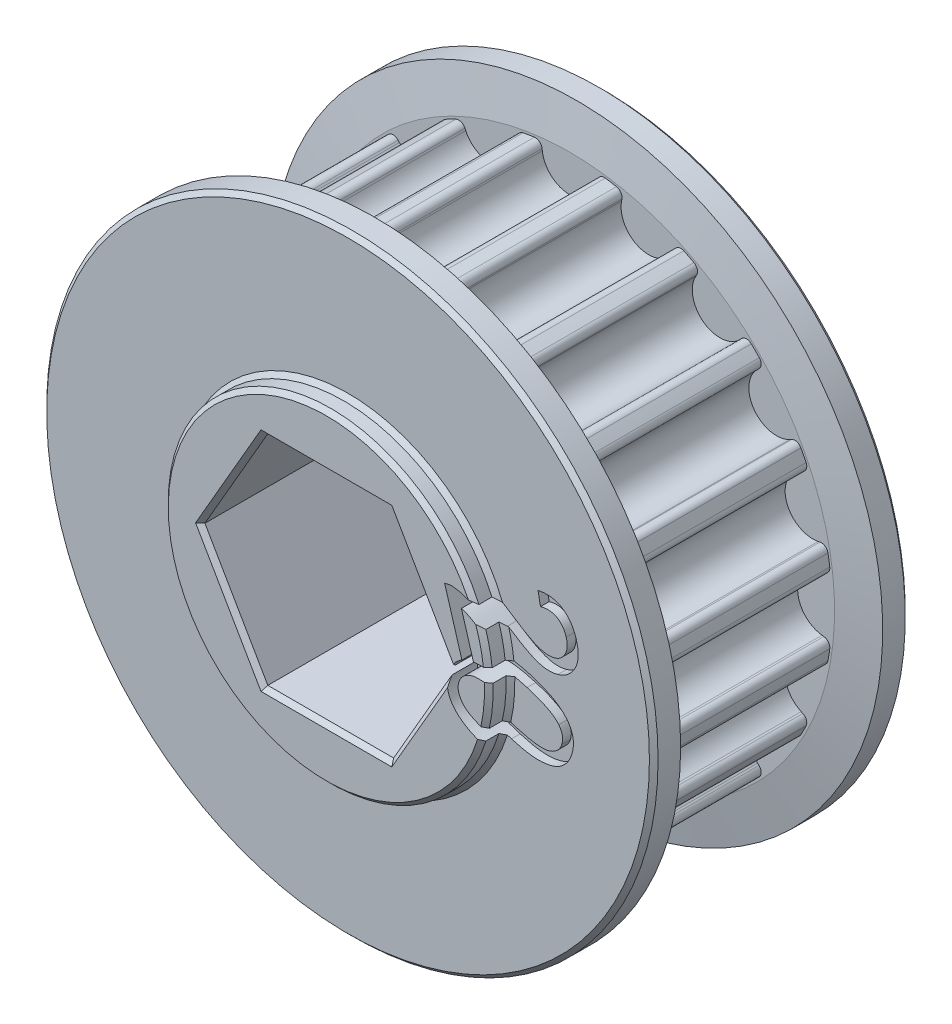
SolidWorks part; units mm, degrees
material "ABS"
ref_plane "Front Plane" through (0, 0, 0) normal (0, 0, 1) x (1, 0, 0)
ref_plane "Top Plane" through (0, 0, 0) normal (0, 1, 0) x (1, 0, 0)
ref_plane "Right Plane" through (0, 0, 0) normal (1, 0, 0) x (0, 0, -1)
sketch "Sketch2" plane through (0, 0, 0) normal (0, 0, 1) x (1, 0, 0)
  circle A0 centre (0, 0) radius 15.3811
extrude "pulley" add sketch "Sketch2" along normal mid plane 11
sketch "tooth" plane through (0, 0, 0) normal (0, 0, 1) x (1, 0, 0)
  line L0 (0, 0) -> (0, 14.9811) construction
  line L1 (4.9299, 14.1467) -> (0, 14.9811) construction
  line L2 (4.9299, 14.1467) -> (0, 0) construction
  line L3 (-2.1327, 19.0167) -> (-1.6129, 14.7831)
  line L6 (2.1327, 19.0167) -> (1.6129, 14.7831)
  line L7 (-2.1327, 19.0167) -> (2.1327, 19.0167)
  arc A1 (-1.6129, 14.7831) -> (1.6129, 14.7831) centre (0, 14.9811) ccw
  arc A2 (0, 14.9811) -> (4.9299, 14.1467) centre (0, 0) cw construction
  circle A3 centre (4.9299, 14.1467) radius 1.625 construction
extrude "cut tooth" cut sketch "tooth" against normal mid plane 11
fillet "blend tooth" radius 0.4 2 edges at (1.6751, 15.2896, 0) (-1.6751, 15.2896, 0)
pattern_circular "tooth pattern" count 20 over 360 about axis through (0, 0, 0) along (0, 0, 1) of "cut tooth", "blend tooth"
sketch "Sketch3" plane through (0, 0, 0) normal (0, 0, 1) x (1, 0, 0)
  circle A0 centre (0, 0) radius 17.9211
  circle A1 centre (0, 0) radius 15.3811 construction
  dimension "D1" = 2.54
extrude "sidewall" add sketch "Sketch3" along normal blind 2 from offset 5.5
mirror "mirror sidewall" about plane through (0, 0, 0) normal (0, 0, 1) of "sidewall"
chamfer "sidewall chamfer" distance 2.4 angle 10 2 edges at (17.9211, 0, 5.5) (17.9211, 0, -5.5)
sketch "Sketch5" plane through (0, 0, 0) normal (0, 0, 1) x (1, 0, 0)
  circle A0 centre (0, 0) radius 9.525
  dimension "D1" = 19.05
extrude "bearing spacer (Manual Suppress)" add sketch "Sketch5" along normal blind 8.77 and the other way blind 8.77
sketch "Sketch4" plane through (0, 0, 0) normal (0, 0, 1) x (1, 0, 0)
  line L1 (3.6882, 6.3881) -> (-3.6882, 6.3881)
  line L2 (-3.6882, 6.3881) -> (-7.3763, 0)
  line L3 (-7.3763, 0) -> (-3.6882, -6.3881)
  line L4 (-3.6882, -6.3881) -> (3.6882, -6.3881)
  line L5 (3.6882, -6.3881) -> (7.3763, 0)
  line L6 (7.3763, 0) -> (3.6882, 6.3881)
  circle A0 centre (0, 0) radius 6.3881 construction
  dimension "D1" = 12.7762
extrude "hex shaft" cut sketch "Sketch4" against normal mid plane 127
chamfer "chamfers" distance 0.254 angle 45 18 edges at (17.9211, 0, -7.5) (17.9211, 0, 7.5) (-9.525, 0, -7.5) (9.525, 0, 7.5) (9.525, 0, 8.77) (0, 6.3881, 8.77) (-5.5323, 3.194, 8.77) (-5.5323, -3.194, 8.77) (0, -6.3881, 8.77) (5.5323, -3.194, 8.77) (5.5323, 3.1941, 8.77) (9.525, 0, -8.77) (0, -6.3881, -8.77) (-5.5323, -3.194, -8.77) (-5.5323, 3.194, -8.77) (0, 6.3881, -8.77) (5.5323, 3.1941, -8.77) (5.5323, -3.194, -8.77)
sketch "SK-VersaCut" plane through (0, 0, 0) normal (0, 0, 1) x (1, 0, 0)
  line B0 (6.3387, 23.6565) -> (5.299, 19.7762)
  line B1 (14.4772, 14.4772) -> (17.3177, 17.3177)
  line B2 (23.6565, 6.3387) -> (19.7762, 5.299)
  line B3 (19.7762, -5.299) -> (23.6565, -6.3387)
  line B4 (17.3177, -17.3177) -> (14.4772, -14.4772)
  line B5 (5.299, -19.7762) -> (6.3387, -23.6565)
  line B6 (-6.3387, -23.6565) -> (-5.299, -19.7762)
  line B7 (-14.4772, -14.4772) -> (-17.3177, -17.3177)
  line B8 (-23.6565, -6.3387) -> (-19.7762, -5.299)
  line B9 (-19.7762, 5.299) -> (-23.6565, 6.3387)
  line B10 (-17.3177, 17.3177) -> (-14.4772, 14.4772)
  line B11 (-5.299, 19.7762) -> (-6.3387, 23.6565)
  circle B12 centre (0, 23.8125) radius 2.2479
  arc B13 (5.9535, 18.5765) -> (13.1109, 14.4442) centre (0, 0) cw
  arc B14 (7.5904, 24.3458) -> (17.2889, 18.7464) centre (0, 0) cw
  arc B15 (5.9535, 18.5765) -> (5.299, 19.7762) centre (6.2559, 19.5198) cw
  arc B16 (13.1109, 14.4442) -> (14.4772, 14.4772) centre (13.7767, 15.1777) ccw
  arc B17 (17.2889, 18.7464) -> (17.3177, 17.3177) centre (16.6173, 18.0182) cw
  arc B18 (7.5904, 24.3458) -> (6.3387, 23.6565) centre (7.2956, 23.4001) ccw
  circle B19 centre (20.6222, 11.9062) radius 2.2479
  arc B20 (19.0645, 4.1323) -> (19.0645, -4.1323) centre (0, 0) cw
  arc B21 (24.8793, 5.5994) -> (24.8793, -5.5994) centre (0, 0) cw
  arc B22 (19.0645, 4.1323) -> (19.7762, 5.299) centre (20.0326, 4.3422) cw
  arc B23 (19.0645, -4.1323) -> (19.7762, -5.299) centre (20.0326, -4.3422) ccw
  arc B24 (24.8793, -5.5994) -> (23.6565, -6.3387) centre (23.9129, -5.3819) cw
  arc B25 (24.8793, 5.5994) -> (23.6565, 6.3387) centre (23.9129, 5.3819) ccw
  circle B26 centre (20.6222, -11.9063) radius 2.2479
  arc B27 (13.1109, -14.4442) -> (5.9535, -18.5765) centre (0, 0) cw
  arc B28 (17.2889, -18.7464) -> (7.5904, -24.3458) centre (0, 0) cw
  arc B29 (13.1109, -14.4442) -> (14.4772, -14.4772) centre (13.7767, -15.1777) cw
  arc B30 (5.9535, -18.5765) -> (5.299, -19.7762) centre (6.2559, -19.5198) ccw
  arc B31 (7.5904, -24.3458) -> (6.3387, -23.6565) centre (7.2956, -23.4001) cw
  arc B32 (17.2889, -18.7464) -> (17.3177, -17.3177) centre (16.6173, -18.0182) ccw
  circle B33 centre (0, -23.8125) radius 2.2479
  arc B34 (-5.9535, -18.5765) -> (-13.1109, -14.4442) centre (0, 0) cw
  arc B35 (-7.5904, -24.3458) -> (-17.2889, -18.7464) centre (0, 0) cw
  arc B36 (-5.9535, -18.5765) -> (-5.299, -19.7762) centre (-6.2559, -19.5198) cw
  arc B37 (-13.1109, -14.4442) -> (-14.4772, -14.4772) centre (-13.7767, -15.1777) ccw
  arc B38 (-17.2889, -18.7464) -> (-17.3177, -17.3177) centre (-16.6173, -18.0182) cw
  arc B39 (-7.5904, -24.3458) -> (-6.3387, -23.6565) centre (-7.2956, -23.4001) ccw
  circle B40 centre (-20.6222, -11.9063) radius 2.2479
  arc B41 (-19.0645, -4.1323) -> (-19.0645, 4.1323) centre (0, 0) cw
  arc B42 (-24.8793, -5.5994) -> (-24.8793, 5.5994) centre (0, 0) cw
  arc B43 (-19.0645, -4.1323) -> (-19.7762, -5.299) centre (-20.0326, -4.3422) cw
  arc B44 (-19.0645, 4.1323) -> (-19.7762, 5.299) centre (-20.0326, 4.3422) ccw
  arc B45 (-24.8793, 5.5994) -> (-23.6565, 6.3387) centre (-23.9129, 5.3819) cw
  arc B46 (-24.8793, -5.5994) -> (-23.6565, -6.3387) centre (-23.9129, -5.3819) ccw
  circle B47 centre (-20.6222, 11.9063) radius 2.2479
  arc B48 (-13.1109, 14.4442) -> (-5.9535, 18.5765) centre (0, 0) cw
  arc B49 (-17.2889, 18.7464) -> (-7.5904, 24.3458) centre (0, 0) cw
  arc B50 (-13.1109, 14.4442) -> (-14.4772, 14.4772) centre (-13.7767, 15.1777) cw
  arc B51 (-5.9535, 18.5765) -> (-5.299, 19.7762) centre (-6.2559, 19.5198) ccw
  arc B52 (-7.5904, 24.3458) -> (-6.3387, 23.6565) centre (-7.2956, 23.4001) cw
  arc B53 (-17.2889, 18.7464) -> (-17.3177, 17.3177) centre (-16.6173, 18.0182) ccw
sketch_block_instance "VersaKey-1"
sketch_block "Block1" parameters "D1"=47.625, "D2"=4.4958, "D3"=19.5072, "D4"=25.5016, "D6"=0.9906, "D5"=30
extrude "VersaKey (Manual Suppress)" [suppressed] cut sketch "SK-VersaCut" against normal through all both and the other way through all
sketch "Lightening Holes" plane through (0, 0, 0) normal (0, 0, 1) x (1, 0, 0)
  line L0 (-2.1942, 8.8805) -> (-3.9521, 11.9253)
  line L1 (3.9521, 11.9253) -> (2.1942, 8.8805)
  line L14 (0, 0) -> (-3.6662, 6.35) construction
  line L15 (0, 0) -> (0, 6.35) construction
  line L24 (0, 0) -> (3.6662, 6.35) construction
  line L25 (0, 6.35) -> (-3.6662, 6.35) construction
  line L26 (0, 6.35) -> (3.6662, 6.35) construction
  line L27 (-3.0943, 11.43) -> (3.0943, 11.43)
  line L28 (0, 6.35) -> (0, 11.43) construction
  line L29 (6.5936, 6.3405) -> (8.3515, 9.3853)
  line L30 (8.3515, 8.3947) -> (11.4458, 3.0353)
  line L31 (12.3037, 2.54) -> (8.7878, 2.54)
  line L32 (8.7878, -2.54) -> (12.3037, -2.54)
  line L33 (11.4458, -3.0353) -> (8.3515, -8.3947)
  line L34 (8.3515, -9.3853) -> (6.5936, -6.3405)
  line L35 (2.1942, -8.8805) -> (3.9521, -11.9253)
  line L36 (3.0943, -11.43) -> (-3.0943, -11.43)
  line L37 (-3.9521, -11.9253) -> (-2.1942, -8.8805)
  line L38 (-6.5936, -6.3405) -> (-8.3515, -9.3853)
  line L39 (-8.3515, -8.3947) -> (-11.4458, -3.0353)
  line L40 (-12.3037, -2.54) -> (-8.7878, -2.54)
  line L41 (-8.7878, 2.54) -> (-12.3037, 2.54)
  line L42 (-11.4458, 3.0353) -> (-8.3515, 8.3947)
  line L43 (-8.3515, 9.3853) -> (-6.5936, 6.3405)
  arc A3 (-1.4761, 10.3565) -> (1.4761, 10.3565) centre (0, 0) cw
  arc A4 (-3.0943, 11.43) -> (-3.9521, 11.9253) centre (-3.0943, 12.4206) cw
  arc A5 (3.0943, 11.43) -> (3.9521, 11.9253) centre (3.0943, 12.4206) ccw
  arc A6 (1.4761, 10.3565) -> (2.1942, 8.8805) centre (1.3363, 9.3758) cw
  arc A7 (-1.4761, 10.3565) -> (-2.1942, 8.8805) centre (-1.3363, 9.3758) ccw
  arc A72 (8.2309, 6.4566) -> (9.707, 3.8999) centre (0, 0) cw
  arc A73 (8.2309, 6.4566) -> (6.5936, 6.3405) centre (7.4515, 5.8452) ccw
  arc A74 (8.3515, 8.3947) -> (8.3515, 9.3853) centre (9.2094, 8.89) cw
  arc A75 (9.707, 3.8999) -> (8.7878, 2.54) centre (8.7878, 3.5306) cw
  arc A76 (9.707, -3.8999) -> (8.2309, -6.4566) centre (0, 0) cw
  arc A77 (9.707, -3.8999) -> (8.7878, -2.54) centre (8.7878, -3.5306) ccw
  arc A78 (11.4458, -3.0353) -> (12.3037, -2.54) centre (12.3037, -3.5306) cw
  arc A79 (8.2309, -6.4566) -> (6.5936, -6.3405) centre (7.4515, -5.8452) cw
  arc A80 (1.4761, -10.3565) -> (-1.4761, -10.3565) centre (0, 0) cw
  arc A81 (1.4761, -10.3565) -> (2.1942, -8.8805) centre (1.3363, -9.3758) ccw
  arc A82 (3.0943, -11.43) -> (3.9521, -11.9253) centre (3.0943, -12.4206) cw
  arc A83 (-1.4761, -10.3565) -> (-2.1942, -8.8805) centre (-1.3363, -9.3758) cw
  arc A84 (-8.2309, -6.4566) -> (-9.707, -3.8999) centre (0, 0) cw
  arc A85 (-8.2309, -6.4566) -> (-6.5936, -6.3405) centre (-7.4515, -5.8452) ccw
  arc A86 (-8.3515, -8.3947) -> (-8.3515, -9.3853) centre (-9.2094, -8.89) cw
  arc A87 (-9.707, -3.8999) -> (-8.7878, -2.54) centre (-8.7878, -3.5306) cw
  arc A88 (-9.707, 3.8999) -> (-8.2309, 6.4566) centre (0, 0) cw
  arc A89 (-9.707, 3.8999) -> (-8.7878, 2.54) centre (-8.7878, 3.5306) ccw
  arc A90 (-11.4458, 3.0353) -> (-12.3037, 2.54) centre (-12.3037, 3.5306) cw
  arc A91 (-8.2309, 6.4566) -> (-6.5936, 6.3405) centre (-7.4515, 5.8452) cw
  arc A92 (11.4458, 3.0353) -> (12.3037, 2.54) centre (12.3037, 3.5306) ccw
  arc A93 (8.3515, -8.3947) -> (8.3515, -9.3853) centre (9.2094, -8.89) ccw
  arc A94 (-3.0943, -11.43) -> (-3.9521, -11.9253) centre (-3.0943, -12.4206) ccw
  arc A95 (-11.4458, -3.0353) -> (-12.3037, -2.54) centre (-12.3037, -3.5306) ccw
  arc A96 (-8.3515, 8.3947) -> (-8.3515, 9.3853) centre (-9.2094, 8.89) ccw
  point P72 (0, 0)
  point P77 (0, 0)
  point P87 (0, 0)
extrude "Lightening Holes (Man Suppress)" [suppressed] cut sketch "Lightening Holes" against normal through all both and the other way through all
sketch "Sketch6" plane through (0, 0, 0) normal (0, 0, 1) x (1, 0, 0)
  line L0 (0, 8.1927) -> (0, 0) construction
  line L1 (0, 0) -> (0, -8.1927) construction
  arc A1 (0, 8.1927) -> (0, -8.1927) centre (0, 0) cw construction
  arc A2 (0, 8.1927) -> (0, -8.1927) centre (0, 0) ccw construction
  text T0 "20\r\n" font "DS-Digital" height in points 24
extrude "4419" cut sketch "Sketch6" along normal blind 2.54 from offset 6.992
equation "\"INPUT_pulley_teeth\"= 20"
equation "\"pulley_c2c\"= 5mm"
equation "\"pulley_teeth_deg\"= 360 / \"INPUT_pulley_teeth\""
equation "\"pulley_radius\"= ( \"pulley_c2c\" / ( 2 * cos ( \"iso_half_angle\" ) ) ) - 1mm"
equation "\"iso_half_angle\"= ( 180 - \"pulley_teeth_deg\" ) / 2"
equation "\"D1@tooth\" = \"pulley_radius\""
equation "\"pulley_tooth_dia\"= 3.25mm"
equation "\"D3@tooth\"=\"pulley_c2c\""
equation "\"D2@tooth\"=\"pulley_tooth_dia\""
equation "\"D1@Sketch2\"=2* \"pulley_radius\"+\"pulley_tooth_offset\""
equation "\"pulley_tooth_offset\"= .8mm"
equation "\"D1@tooth pattern\" = \"INPUT_pulley_teeth\""
equation "\"INPUT_pulley_belt_9_or_15_(unitless)\"= 9"
equation "\"D1@pulley\"=\"pulley_width\""
equation "\"D19@sidewall\" =  ( \"pulley_width\" / 2 ) "
equation "\"D1@sidewall\"=\"pulley_sidewall_thick\""
equation "\"pulley_width\"= IIF ( \"INPUT_pulley_belt_9_or_15_(unitless)\" = 9 , 11mm , 17mm )"
equation "\"D1@cut tooth\"=\"pulley_width\""
equation "\"D1@sidewall chamfer\" = 2.4mm"
equation "\"D4@Lightening Holes\"=\"pulley_radius\"-\"pulley_tooth_dia\"-.05"
equation "\"D1@bearing spacer (Manual Suppress)\" = 0.05 +  ( \"pulley_width\" / 2 )  + \"pulley_sidewall_thick\""
equation "\"D2@bearing spacer (Manual Suppress)\" = 0.05 +  ( \"pulley_width\" / 2 )  + \"pulley_sidewall_thick\""
equation "\"pulley_sidewall_thick\"= 2mm"
equation "\"D1@4419\" = \"pulley_width\""
equation "\"D19@4419\"=(\"pulley_width\" / 2) +\"pulley_sidewall_thick\" - 0.02"
equation "\"rad_len\" = \"INPUT_pulley_teeth\" * \"pulley_c2c\""
